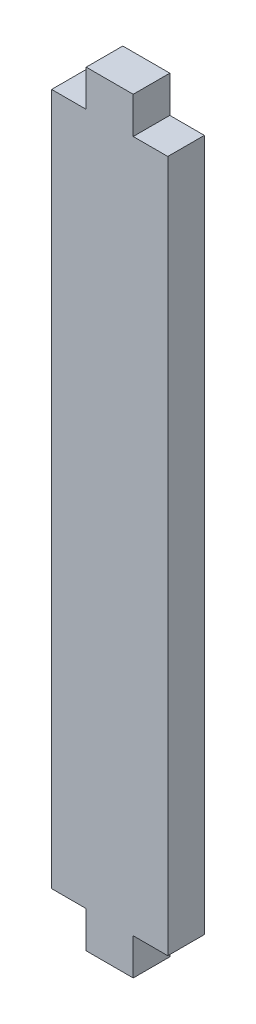
SolidWorks part; units mm, degrees
ref_plane "Front Plane" through (0, 0, 0) normal (0, 0, 1) x (1, 0, 0)
ref_plane "Top Plane" through (0, 0, 0) normal (0, 1, 0) x (1, 0, 0)
ref_plane "Right Plane" through (0, 0, 0) normal (1, 0, 0) x (0, 0, -1)
sketch "Sketch1" plane through (0, 0, 0) normal (0, 0, 1) x (1, 0, 0)
  line L0 (-2, -33.175) -> (-2, -30)
  line L1 (-5, 30) -> (5, 30)
  line L2 (-5, 30) -> (-5, -30)
  line L3 (-5, -30) -> (5, -30)
  line L4 (5, 30) -> (5, -30)
  line L5 (-2, -33.175) -> (2, -33.175)
  line L6 (-2, -30) -> (2, -30)
  line L7 (2, -33.175) -> (2, -30)
  line L8 (-2, -33.175) -> (2, -30) construction
  line L9 (-2, -30) -> (2, -33.175) construction
  line L10 (-5, 0) -> (5, 0) construction
  line L11 (-2, 30) -> (2, 33.175) construction
  line L12 (-2, 33.175) -> (2, 30) construction
  line L13 (2, 33.175) -> (2, 30)
  line L14 (-2, 33.175) -> (2, 33.175)
  line L15 (-2, 33.175) -> (-2, 30)
  point P5 (0, -30)
  point P6 (0, -31.5875)
  point P17 (0, 31.5875)
  dimension "D1" = 60
  dimension "D2" = 10
  dimension "D3" = 5
  dimension "D4" = 30
  dimension "D5" = 4
  dimension "D6" = 3.175
extrude "Boss-Extrude1" add sketch "Sketch1" along normal blind 3.175 contours L4 L1 L2 L3 | L14 L15 L1 L13 | L5 L7 L3 L0
sketch "Sketch2" plane through (0, 0, 3.175) normal (0, 0, 1) x (1, 0, 0)
  line L24 (5.0406, -30.0406) -> (5.0406, 30.0406)
  line L25 (5.0406, 30.0406) -> (2.0406, 30.0406)
  line L26 (2.0406, 30.0406) -> (2.0406, 33.2156)
  line L27 (2.0406, 33.2156) -> (-2.0406, 33.2156)
  line L28 (-2.0406, 33.2156) -> (-2.0406, 30.0406)
  line L29 (-2.0406, 30.0406) -> (-5.0406, 30.0406)
  line L30 (-5.0406, 30.0406) -> (-5.0406, -30.0406)
  line L31 (-5.0406, -30.0406) -> (-2.0406, -30.0406)
  line L32 (-2.0406, -30.0406) -> (-2.0406, -33.2156)
  line L33 (-2.0406, -33.2156) -> (2.0406, -33.2156)
  line L34 (2.0406, -33.2156) -> (2.0406, -30.0406)
  line L35 (2.0406, -30.0406) -> (5.0406, -30.0406)
  line L36 (5.0406, -30.0406) -> (5.0406, 30.0406)
  line L37 (5.0406, 30.0406) -> (2.0406, 30.0406)
  line L38 (2.0406, 30.0406) -> (2.0406, 33.2156)
  line L39 (2.0406, 33.2156) -> (-2.0406, 33.2156)
  line L40 (-2.0406, 33.2156) -> (-2.0406, 30.0406)
  line L41 (-2.0406, 30.0406) -> (-5.0406, 30.0406)
  line L42 (-5.0406, 30.0406) -> (-5.0406, -30.0406)
  line L43 (-5.0406, -30.0406) -> (-2.0406, -30.0406)
  line L44 (-2.0406, -30.0406) -> (-2.0406, -33.2156)
  line L45 (-2.0406, -33.2156) -> (2.0406, -33.2156)
  line L46 (2.0406, -33.2156) -> (2.0406, -30.0406)
  line L47 (2.0406, -30.0406) -> (5.0406, -30.0406)
  dimension "D1" = 0.0406
extrude "Boss-Extrude2" add sketch "Sketch2" against normal blind 3.175
equation "\"stepper width\"=4.23"
equation "\"stepper hole disctance\" = 3.1"
equation "\"stepper hole diameter\"=0.34"
equation "\"stepper shaft hole\"=2.4"
equation "\"tooth width\"=0.4"
equation "\"tooth thickness\"=0.3175"
equation "\"tooth to side\"=0.75"
equation "\"motor chamber height\" = 6"
equation "\"D1@Sketch1\"=\"motor chamber height\""
equation "\"holding wall width\"=1"
equation "\"D2@Sketch1\"=\"holding wall width\""
equation "\"D3@Sketch1\"=\"holding wall width\"/2"
equation "\"D4@Sketch1\"=\"motor chamber height\"/2"
equation "\"D5@Sketch1\"=\"tooth width\""
equation "\"D6@Sketch1\"=\"tooth thickness\""
equation "\"D1@Boss-Extrude1\"=\"tooth thickness\""
